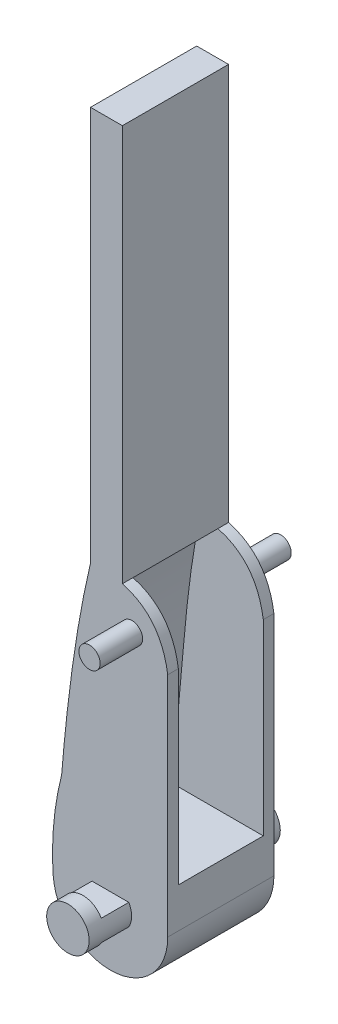
SolidWorks part; units mm, degrees
ref_plane "前视基准面" through (0, 0, 0) normal (0, 0, 1) x (1, 0, 0)
ref_plane "上视基准面" through (0, 0, 0) normal (0, 1, 0) x (1, 0, 0)
ref_plane "右视基准面" through (0, 0, 0) normal (1, 0, 0) x (0, 0, -1)
sketch "草图1" plane through (0, 0, 0) normal (0, 0, 1) x (1, 0, 0)
  line L0 (0, 23.2686) -> (0, -23.2686) construction
  line L9 (-11, -0.6563) -> (-11, -22.43)
  line L10 (-6.0619, 12.0265) -> (-10.0392, 3.6207)
  line L11 (-5.1011, 23.2686) -> (-5.1011, 16.3035)
  arc A2 (-21.7863, -22.8033) -> (-11, -22.43) centre (-16.3996, -22.43) ccw
  arc A4 (-11, -0.6563) -> (-10.0392, 3.6207) centre (-1, -0.6563) cw
  arc A5 (-6.0619, 12.0265) -> (-5.1011, 16.3035) centre (-15.1011, 16.3035) ccw
  spline S1 degree 2 poles (-20.9921, -14.1978) (-22.084, -18.5085) (-21.7863, -22.8033) knots 0 0 0 0.849529 0.849529 0.849529
  spline S3 degree 3 poles (-20.9921, -14.1978) (-19.9825, -1.8352) (-16.9113, 22.3154) (-5.1011, 23.2686) knots 0.32526 0.32526 0.32526 0.32526 1 1 1 1
  point P3 (0, 0)
  point P7 (0, 0)
extrude "凸台-拉伸1" add sketch "草图1" along normal mid plane 10
sketch "草图3" plane through (0, 0, 5) normal (0, 0, 1) x (1, 0, 0)
  circle A0 centre (-16.3996, -22.43) radius 2
  circle A1 centre (-14.3665, 0.7061) radius 1
  dimension "D1" = 4
  dimension "D2" = 2
extrude "凸台-拉伸2" add sketch "草图3" along normal blind 4 and the other way blind 14
sketch "草图2" plane through (0, 0, 0) normal (0, 0, 1) x (1, 0, 0)
  line L0 (-14.1606, 12.8081) -> (14.1606, 12.8081)
  line L1 (-19.7287, -18.6752) -> (19.7287, -18.6752)
  line L2 (0, 0) -> (0, 4.078) construction
  spline S0 degree 3 poles (-14.1606, 12.8081) (-18.7957, 3.0124) (-18.1519, -8.2138) (-19.7287, -18.6752) knots 0 0 0 0 1 1 1 1
  spline S1 degree 3 poles (14.1606, 12.8081) (18.7957, 3.0124) (18.1519, -8.2138) (19.7287, -18.6752) knots 0 0 0 0 1 1 1 1
  point P3 (0, 12.8081)
  point P6 (0, -18.6752)
extrude "切除-拉伸1" cut sketch "草图2" against normal mid plane 8
sketch "草图4" plane through (0, 0, 0) normal (1, 0, 0) x (0, 0, -1)
  line L0 (-9, -20.43) -> (-9, -24.43) construction
  line L1 (0, -18.6752) -> (0, -21.383) construction
  line L2 (4, -18.6752) -> (-4, -18.6752) construction
  line L3 (-5, -20.43) -> (-5, -24.43) construction
  line L4 (-7.591, -19.479) -> (-5, -19.479)
  line L5 (-7.591, -19.479) -> (-7.591, -21.43)
  line L6 (-7.591, -21.43) -> (-5, -21.43)
  line L7 (-5, -19.479) -> (-5, -21.43)
  line L8 (-5, -22.43) -> (-5, -27.8296) construction
  line L9 (-5, -25.6158) -> (-7.591, -25.6158)
  line L10 (-5, -25.6158) -> (-5, -23.43)
  line L11 (-5, -23.43) -> (-7.591, -23.43)
  line L12 (-7.591, -25.6158) -> (-7.591, -23.43)
  line L13 (7.591, -25.6158) -> (7.591, -23.43)
  line L14 (5, -23.43) -> (7.591, -23.43)
  line L15 (5, -25.6158) -> (5, -23.43)
  line L16 (5, -25.6158) -> (7.591, -25.6158)
  line L17 (5, -19.479) -> (5, -21.43)
  line L18 (7.591, -21.43) -> (5, -21.43)
  line L19 (7.591, -19.479) -> (7.591, -21.43)
  line L20 (7.591, -19.479) -> (5, -19.479)
  dimension "D1" = 1
  dimension "D2" = 1
extrude "切除-拉伸2" cut sketch "草图4" against normal through all both and the other way through all
sketch "草图5" plane through (0, 0, 5) normal (0, 0, 1) x (1, 0, 0)
  line L1 (-27.6764, 30.9626) -> (3.6044, 30.9626)
  line L2 (-27.6764, 30.9626) -> (-27.6764, 4.4534)
  line L3 (-27.6764, 4.4534) -> (3.6044, 4.4534)
  line L4 (3.6044, 30.9626) -> (3.6044, 4.4534)
extrude "切除-拉伸3" cut sketch "草图5" against normal blind 10
sketch "草图6" plane through (0, 0, 5) normal (0, 0, 1) x (1, 0, 0)
  line L0 (-18.2712, 4.4534) -> (-9.6452, 4.4534) construction
  line L1 (-11, -22.43) -> (-11, -0.6563) construction
  line L2 (-11, -1.0308) -> (-7.2894, 0)
  line L3 (-7.2894, 0) -> (-6.6276, 7.0548)
  line L4 (-6.6276, 7.0548) -> (-15.0009, 5.8463)
  line L5 (-15.0009, 5.8463) -> (-16.2382, 4.4534)
  spline S0 degree 2 poles (-16.2382, 4.4534) (-11.718, 3.7971) (-11, -1.0308) knots 0 0 0 1 1 1
extrude "切除-拉伸4" cut sketch "草图6" against normal blind 10
sketch "草图7" plane through (0, 0, 5) normal (0, 0, 1) x (1, 0, 0)
  line L0 (-18.2712, 4.4534) -> (-18.2712, 41.6164)
  line L1 (-18.2712, 41.6164) -> (-15.2712, 41.6164)
  line L2 (-15.2712, 41.6164) -> (-15.2712, 4.2535)
  line L3 (-18.2712, 4.4534) -> (-15.2712, 4.2535)
  parabola Q0 (-16.2382, 4.4534) -> (-11, -1.0308) focus (-14.6279, 1.1263) apex (-12.9201, 3) construction
extrude "凸台-拉伸4" add sketch "草图7" against normal up to surface (10 mm away)
